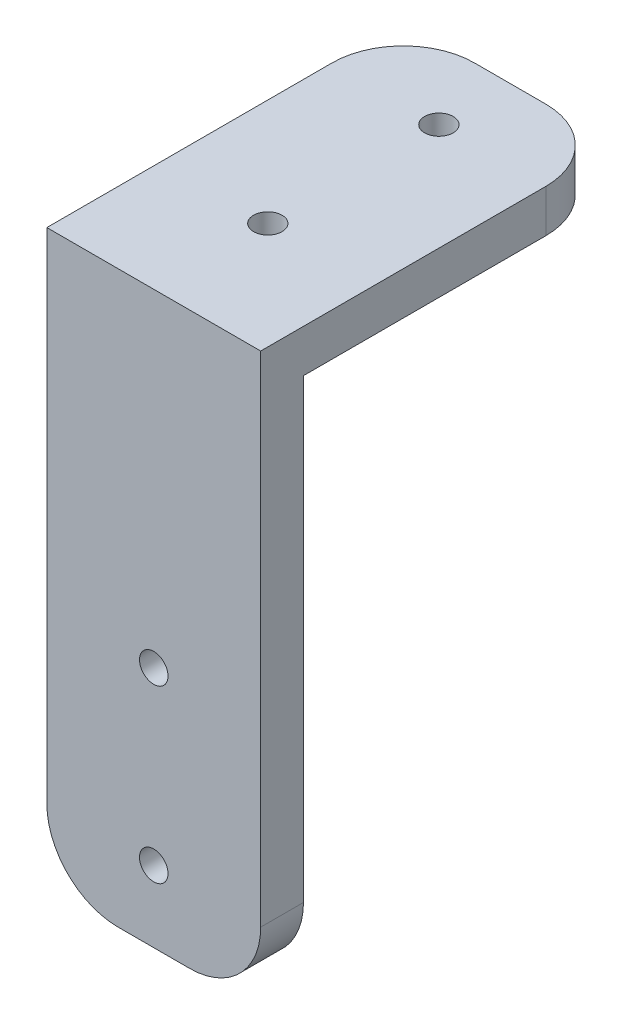
SolidWorks part; units mm, degrees
ref_plane "前视基准面" through (0, 0, 0) normal (0, 0, 1) x (1, 0, 0)
ref_plane "上视基准面" through (0, 0, 0) normal (0, 1, 0) x (1, 0, 0)
ref_plane "右视基准面" through (0, 0, 0) normal (1, 0, 0) x (0, 0, -1)
sketch "草图1" plane through (0, 0, 0) normal (0, 0, 1) x (1, 0, 0)
  line L1 (5, 0) -> (10, 0)
  line L2 (0, 5) -> (0, 40)
  line L3 (0, 40) -> (15, 40)
  line L4 (15, 5) -> (15, 40)
  circle A0 centre (7.5, 5) radius 1
  arc A1 (5, 0) -> (0, 5) centre (5, 5) cw
  arc A2 (10, 0) -> (15, 5) centre (10, 5) ccw
  circle A3 centre (7.5, 17) radius 1
  point P9 (0, 0)
  point P12 (15, 0)
  dimension "D3" = 2
  dimension "D4" = 5
  dimension "D5" = 5
  dimension "D7" = 2
  dimension "D1" = 15
  dimension "D2" = 40
  dimension "D6" = 5
  dimension "D8" = 12
extrude "凸台-拉伸1" add sketch "草图1" along normal blind 3
ref_plane "基准面1" through (0, 40, 0) normal (0, -1, 0) x (-1, 0, 0)
sketch "草图2" plane through (0, 40, 0) normal (0, -1, 0) x (-1, 0, 0)
  line L1 (-15, -3) -> (0, -3)
  line L2 (-15, -3) -> (-15, 17)
  line L3 (-10, 22) -> (-5, 22)
  line L4 (0, -3) -> (0, 17)
  circle A0 centre (-7.5, 17) radius 1
  circle A1 centre (-7.5, 5) radius 1
  arc A2 (-15, 17) -> (-10, 22) centre (-10, 17) cw
  arc A3 (-5, 22) -> (0, 17) centre (-5, 17) cw
  point P11 (-15, 22)
  dimension "D2" = 2
  dimension "D3" = 2
  dimension "D6" = 5
  dimension "D1" = 25
  dimension "D4" = 5
  dimension "D5" = 12
extrude "凸台-拉伸2" add sketch "草图2" along normal blind 3
